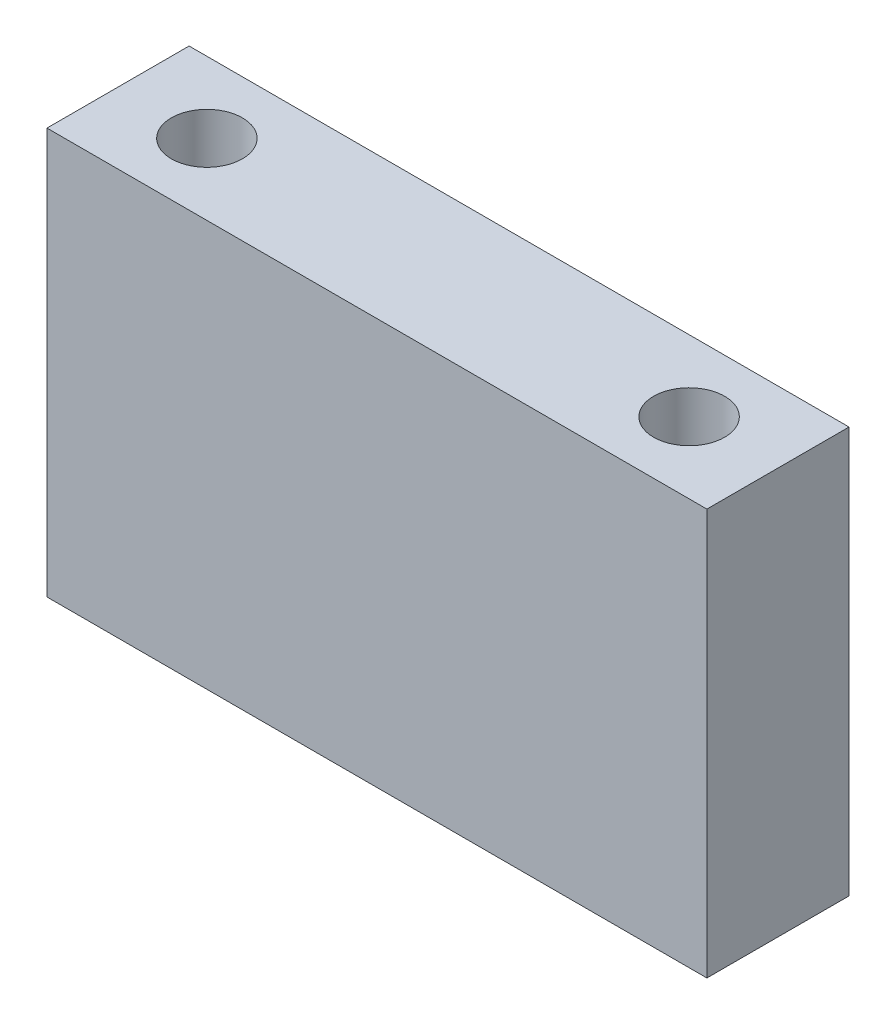
SolidWorks part; units mm, degrees
ref_plane "Plan de face" through (0, 0, 0) normal (0, 0, 1) x (1, 0, 0)
ref_plane "Plan de dessus" through (0, 0, 0) normal (0, 1, 0) x (1, 0, 0)
ref_plane "Plan de droite" through (0, 0, 0) normal (1, 0, 0) x (0, 0, -1)
sketch "Sketch1" plane through (0, 0, 0) normal (0, 0, 1) x (1, 0, 0)
  line L1 (0, 0) -> (65, 0)
  line L2 (0, 0) -> (0, 40)
  line L3 (0, 40) -> (65, 40)
  line L4 (65, 0) -> (65, 40)
  dimension "D1" = 65
  dimension "D2" = 40
extrude "Extrude1" add sketch "Sketch1" along normal blind 14
sketch "Sketch2" plane through (0, 40, 0) normal (0, 1, 0) x (1, 0, 0)
  line L0 (0, -7) -> (65, -7) construction
  line L1 (0, -14) -> (0, 0) construction
  line L2 (65, -14) -> (65, 0) construction
  line L3 (32.5, 0) -> (32.5, -14) construction
  line L4 (65, 0) -> (0, 0) construction
  line L5 (65, -14) -> (0, -14) construction
  circle A0 centre (8.75, -7) radius 3.5
  circle A1 centre (56.25, -7) radius 3.5
  point P16 (0, 0)
  dimension "D1" = 7
  dimension "D2" = 47.5
extrude "Extrude2" cut sketch "Sketch2" against normal through all
